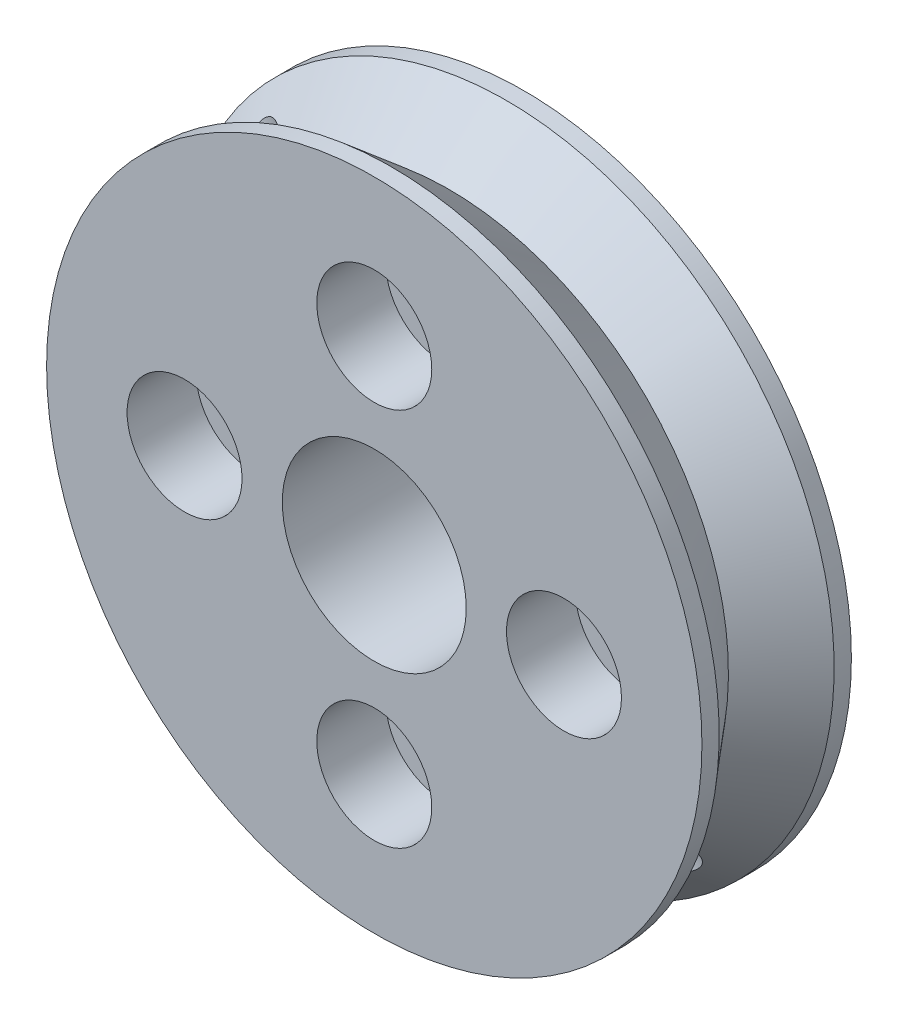
SolidWorks part; units mm, degrees
ref_plane "Plan de face" through (0, 0, 0) normal (0, 0, 1) x (1, 0, 0)
ref_plane "Plan de dessus" through (0, 0, 0) normal (0, 1, 0) x (1, 0, 0)
ref_plane "Plan de droite" through (0, 0, 0) normal (1, 0, 0) x (0, 0, -1)
sketch "Esquisse2" plane through (0, 0, 0) normal (0, 0, 1) x (1, 0, 0)
  circle A0 centre (0, 0) radius 14.25
  circle A1 centre (0, 0) radius 8.25
  dimension "D1" = 28.5
  dimension "D2" = 16.5
extrude "Boss.-Extru.1" add sketch "Esquisse2" along normal mid plane 6.5 contours A0
sketch "Esquisse3" plane through (0, 0, 0) normal (0, 0, 1) x (1, 0, 0)
  circle A2 centre (0, 8.25) radius 1.2
  circle A3 centre (-8.25, 0) radius 1.2
  circle A4 centre (0, -8.25) radius 1.2
  circle A5 centre (8.25, 0) radius 1.2
  point P3 (-8.25, 0)
  point P11 (0, 8.25)
  point P12 (8.25, 0)
  point P13 (0, -8.25)
  dimension "D1" = 2.4
  dimension "D2" = 2.4
  dimension "D3" = 2.4
  dimension "D4" = 2.4
extrude "Enlèv. mat.-Extru.1" cut sketch "Esquisse3" along normal through all
sketch "Esquisse10" plane through (0, 0, -3.25) normal (0, 0, -1) x (-1, 0, 0)
  circle A0 centre (-8.25, 0) radius 1.7
  circle A1 centre (0, 8.25) radius 1.7
  circle A2 centre (8.25, 0) radius 1.7
  circle A3 centre (0, -8.25) radius 1.7
  dimension "D1" = 3.4
  dimension "D2" = 3.4
  dimension "D3" = 3.4
  dimension "D4" = 3.4
extrude "Enlèv. mat.-Extru.2" cut sketch "Esquisse10" against normal through all and the other way through all
sketch "Esquisse11" plane through (0, 0, -3.25) normal (0, 0, -1) x (-1, 0, 0)
  line L0 (0, 0) -> (0, -14.25)
  line L1 (0, -14.25) -> (0, 0)
  line L2 (-14.25, 0) -> (0, 0)
  line L3 (0, 0) -> (-10.0763, -10.0763)
  line L4 (-10.0763, -10.0763) -> (10.0763, 10.0763)
  line L5 (-10.0763, -10.0763) -> (-13.3052, -6.8474)
  line L6 (-13.3052, -6.8474) -> (-7.1266, -13.0259)
  circle A0 centre (0, 0) radius 14.25 construction
ref_plane "Plan1" through (10.0763, -10.0763, 0) normal (0.7071, -0.7071, 0) x (-0.7071, -0.7071, 0)
sketch "Esquisse13" plane through (10.0763, -10.0763, 0) normal (0.7071, -0.7071, 0) x (-0.7071, -0.7071, 0)
  line L0 (0, 0) -> (0, -3.25)
  line L1 (-14.25, -3.25) -> (14.25, -3.25) construction
  circle A1 centre (0, 0) radius 1.4
  dimension "D1" = 3.25
  dimension "D2" = 2.8
sketch "Esquisse16" plane through (0, 0, 3.25) normal (0, 0, 1) x (1, 0, 0)
  line L0 (0, 0) -> (-6.1179, -5.0018)
sketch "Esquisse17" plane through (0, 0, 3.25) normal (0, 0, 1) x (1, 0, 0)
  circle A0 centre (0, 0) radius 4
  dimension "D1" = 8
extrude "Enlèv. mat.-Extru.8" cut sketch "Esquisse17" against normal through all
sketch "Esquisse14" plane through (0, 0, 0) normal (0, 0, 1) x (1, 0, 0)
  circle A0 centre (0, 0) radius 11.75
  circle A1 centre (0, 0) radius 14.25
  dimension "D1" = 23.5
extrude "Enlèv. mat.-Extru.4" cut sketch "Esquisse13" against normal through all contours A1
sketch "Esquisse18" plane through (0, 0, 0) normal (0, 1, 0) x (1, 0, 0)
  line L0 (14.25, 2.5) -> (12.1523, 0)
  line L1 (14.25, -3.25) -> (14.25, 3.25) construction
  line L2 (12.1523, 0) -> (14.25, -2.5)
  line L3 (14.25, -2.5) -> (14.25, 2.5)
  line L4 (-14.25, 0) -> (14.25, 0) construction
  line L5 (12.1523, 0) -> (13.5956, 0) construction
  point P4 (14.25, 0)
  point P10 (12.1523, 0)
  dimension "D1" = 40
  dimension "D2" = 40
  dimension "D3" = 5
  dimension "D4" = 1.4434
sketch "Esquisse19" plane through (0, 0, 0) normal (1, 0, 0) x (0, 0, -1)
  line L0 (3.25, 0) -> (-5.3209, 0) construction
revolve "Enlèvement de matière-Révolution1" cut sketch "Esquisse18" angle 360 about L0
ref_plane "Plan2" through (-9.5257, 7.5458, 0) normal (0.6209, 0.7839, 0) x (0.7839, -0.6209, 0)
sketch "Esquisse20" plane through (0, 0, 3.25) normal (0, 0, 1) x (1, 0, 0)
  circle A0 centre (0, 8.25) radius 2.5
  circle A1 centre (8.25, 0) radius 2.5
  circle A2 centre (-8.25, 0) radius 2.5
  circle A3 centre (0, -8.25) radius 2.5
  dimension "D1" = 5
extrude "Enlèv. mat.-Extru.9" cut sketch "Esquisse20" against normal blind 3
